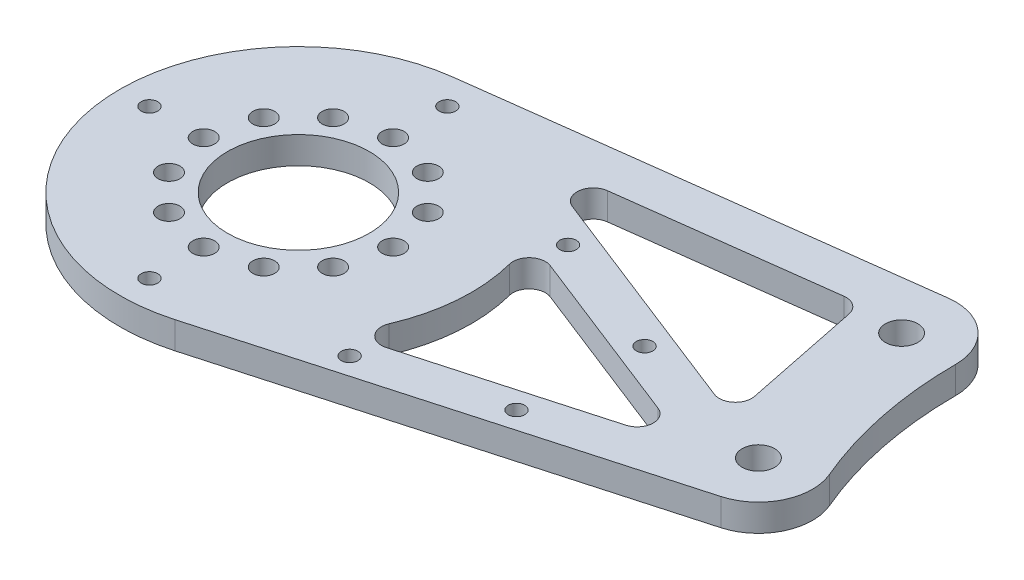
SolidWorks part; units mm, degrees
material "Thornel Mat VMA"
ref_plane "前视基准面" through (0, 0, 0) normal (0, 0, 1) x (1, 0, 0)
ref_plane "上视基准面" through (0, 0, 0) normal (0, 1, 0) x (1, 0, 0)
ref_plane "右视基准面" through (0, 0, 0) normal (1, 0, 0) x (0, 0, -1)
other "Configuration Table"
sketch "草图1" plane through (0, 0, 0) normal (0, 1, 0) x (1, 0, 0)
  line L0 (0, 0) -> (85, 0) construction
  line L1 (0, 0) -> (78.2429, 33.2121) construction
  line L2 (8.9294, -31.7689) -> (87.7059, -9.627)
  line L3 (-4.1935, 32.7325) -> (76.9721, 43.1311)
  circle A0 centre (0, 0) radius 13.1
  circle A1 centre (0, 0) radius 17.5 construction
  circle A2 centre (0, 17.5) radius 2.025
  circle A3 centre (8.75, 15.1554) radius 2.025
  circle A4 centre (15.1554, 8.75) radius 2.025
  circle A5 centre (17.5, 0) radius 2.025
  circle A6 centre (15.1554, -8.75) radius 2.025
  circle A7 centre (8.75, -15.1554) radius 2.025
  circle A8 centre (0, -17.5) radius 2.025
  circle A9 centre (-8.75, -15.1554) radius 2.025
  circle A10 centre (-15.1554, -8.75) radius 2.025
  circle A11 centre (-17.5, 0) radius 2.025
  circle A12 centre (-15.1554, 8.75) radius 2.025
  circle A13 centre (-8.75, 15.1554) radius 2.025
  circle A14 centre (0, 0) radius 33
  circle A15 centre (85, 0) radius 3
  circle A16 centre (78.2429, 33.2121) radius 3
  circle A17 centre (78.2429, 33.2121) radius 10
  circle A18 centre (85, 0) radius 10
  circle A19 centre (163.2429, 33.2121) radius 75
  point P31 (0, 0)
  dimension "D1" = 26.2
  dimension "D2" = 35
  dimension "D3" = 4.05
  dimension "D5" = 66
  dimension "D6" = 6
  dimension "D9" = 20
  dimension "D10" = 150
  dimension "D7" = 85
  dimension "D8" = 23
  dimension "D4" = 12
extrude "凸台-拉伸1" add sketch "草图1" along normal blind 5 contours A19 A17 L3 A14 L2 A18 | A14 A0 A2 A3 A4 A5 A6 A7 A8 A9 A10 A11 A12 A13 | A18 A15 | A17 A16
sketch "草图4" plane through (0, 0, 0) normal (0, -1, 0) x (1, 0, 0)
  line L0 (85, 0) -> (78.2429, -33.2121) construction
  line L1 (25.9945, 18.6624) -> (76.1087, 4.5766)
  line L2 (28.7852, -13.979) -> (76.1087, 4.5766)
  line L8 (16.6361, -27.3357) -> (75.8816, -4.1055)
  line L9 (75.8816, -4.1055) -> (69.7704, -34.143)
  line L10 (69.7704, -34.143) -> (16.6361, -27.3357)
  line L11 (-4.1935, -32.7325) -> (76.9721, -43.1311) construction
  line L12 (8.9294, 31.7689) -> (87.7059, 9.627) construction
  circle A1 centre (0, 0) radius 32
  circle A2 centre (85, 0) radius 10
  dimension "D1" = 20
  dimension "D2" = 64
  dimension "D3" = 8
  dimension "D4" = 8
  dimension "D5" = 8
extrude "切除-拉伸3" cut sketch "草图4" against normal blind 10 contours A1 L2 L1 | L10 L9 L8
fillet "圆角2" radius 3 6 edges at (75.8816, 2.5, -4.1055) (16.6361, 2.5, -27.3357) (76.1087, 2.5, 4.5766) (28.7852, 2.5, -13.979) (25.9945, 2.5, 18.6624) (69.7704, 2.5, -34.143)
sketch "草图5" plane through (0, 5, 0) normal (0, 1, 0) x (1, 0, 0)
  line L0 (88.6634, -5.2028) -> (10.0468, 25.6229) construction
  line L1 (88.6634, -5.2028) -> (4.4013, -28.8867) construction
  line L2 (67.5045, -6.995) -> (32.9705, -16.7016) construction
  line L3 (67.7878, -1.314) -> (34.9821, 11.5492) construction
  circle A0 centre (0, 0) radius 27.5222 construction
  circle A1 centre (-27.5222, 0) radius 1.525
  circle A2 centre (0, 27.5222) radius 1.525
  circle A3 centre (0, -27.5222) radius 1.525
  circle A4 centre (30.9017, -21.4381) radius 1.525
  circle A5 centre (54.9691, -14.6734) radius 1.525
  circle A6 centre (33.3215, 16.4968) radius 1.525
  circle A7 centre (56.5963, 7.3707) radius 1.525
  dimension "D3" = 3.05
  dimension "D4" = 25
  dimension "D6" = 25
  dimension "D7" = 35
  dimension "D1" = 4
  dimension "D2" = 4
  dimension "D5" = 25
extrude "切除-拉伸4" cut sketch "草图5" against normal blind 20
